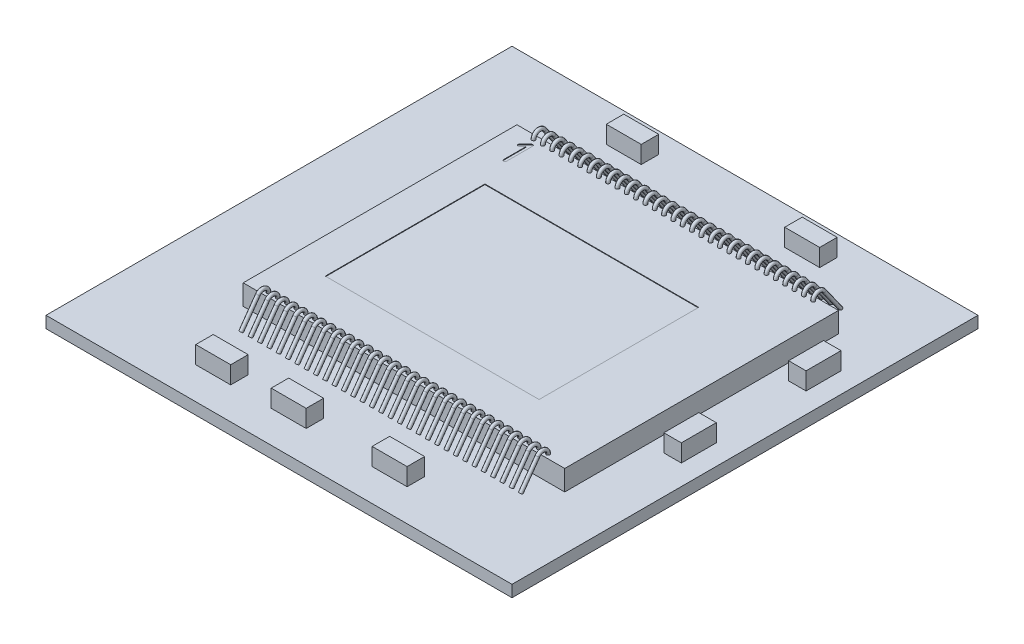
SolidWorks part; units mm, degrees
material "1060 Legierung"
ref_plane "Vorne" through (0, 0, 0) normal (0, 0, 1) x (1, 0, 0)
ref_plane "Oben" through (0, 0, 0) normal (0, 1, 0) x (1, 0, 0)
ref_plane "Rechts" through (0, 0, 0) normal (1, 0, 0) x (0, 0, -1)
ref_plane "Faser-Ebene_Vorne" through (0, 0, 0.175) normal (0, 0, 1) x (1, 0, 0)
ref_plane "Faser-Ebene_Rechts" through (-0.32, 0, 0) normal (1, 0, 0) x (0, 0, -1)
sketch "X-Ray_side"
sketch "Chip_Dimensions"
sketch "Skizze1" plane through (0, 0, 0) normal (0, 1, 0) x (1, 0, 0)
  line L0 (-2.76, 2.35) -> (2.76, -2.35) construction
  line L1 (-2.76, 2.35) -> (2.76, 2.35)
  line L2 (-2.76, 2.35) -> (-2.76, -2.35)
  line L3 (-2.76, -2.35) -> (2.76, -2.35)
  line L4 (2.76, 2.35) -> (2.76, -2.35)
  dimension "D1" = 5.52
  dimension "D2" = 4.7
extrude "Chip_Die" add sketch "Skizze1" along normal blind 0.35
sketch "Skizze4" plane through (0, 0.35, 0) normal (0, 1, 0) x (1, 0, 0)
  line L0 (1.515, 1.195) -> (-2.155, -1.545) construction
  line L1 (-2.155, 1.195) -> (1.515, 1.195)
  line L2 (-2.155, 1.195) -> (-2.155, -1.545)
  line L3 (-2.155, -1.545) -> (1.515, -1.545)
  line L4 (1.515, 1.195) -> (1.515, -1.545)
  line L5 (-0.32, 1.195) -> (-0.32, -0.1113) construction
  line L7 (-0.32, -0.1925) -> (-0.32, 0.1925) construction
  line L8 (1.515, -0.175) -> (0.7734, -0.175) construction
  line L9 (-0.1925, -0.175) -> (0.1925, -0.175) construction
  point P6 (-0.32, -0.175)
  point P7 (0, 0)
  dimension "D1" = 3.67
  dimension "D2" = 2.74
extrude "Active_Area" cut sketch "Skizze4" against normal blind 0.01
sketch "Skizze5" plane through (0, 0.35, 0) normal (0, 1, 0) x (1, 0, 0)
  text T0 "1" font "ISOCPEUR" height 0.5
extrude "Pin1" cut sketch "Skizze5" against normal blind 0.01
sketch "Skizze6" plane through (0, 0, 0) normal (0, 1, 0) x (1, 0, 0)
  line L0 (-2.155, 1.195) -> (1.515, -1.545) construction
  line L1 (-4.32, 3.825) -> (3.68, 3.825)
  line L2 (-4.32, 3.825) -> (-4.32, -4.175)
  line L3 (-4.32, -4.175) -> (3.68, -4.175)
  line L4 (3.68, 3.825) -> (3.68, -4.175)
  line L5 (3.68, 3.825) -> (-4.32, -4.175) construction
  point P7 (-0.32, -0.175)
  dimension "D1" = 8
extrude "Base-Plate" add sketch "Skizze6" against normal blind 0.2
sketch "Skizze12" plane through (0, 0, 0) normal (1, 0, 0) x (0, 0, -1)
  line L0 (-2.35, 0.35) -> (2.35, 0.35) construction
  line L1 (-2.4563, 0.4079) -> (-2.7458, 0)
  line L2 (-4.175, 0) -> (3.825, 0) construction
  line L3 (0, 0) -> (0, 1.1196) construction
  arc A0 (-2.2748, 0.35) -> (-2.4563, 0.4079) centre (-2.3748, 0.35) ccw
  dimension "D1" = 0.1
sketch "Skizze13" plane through (0, 0.35, 0) normal (0, 1, 0) x (1, 0, 0)
  line L0 (0, 0) -> (0, -1.1473) construction
  circle A0 centre (0, -2.2748) radius 0.03
  circle A1 centre (0.16, -2.2748) radius 0.03
  circle A2 centre (0.32, -2.2748) radius 0.03
  circle A3 centre (0.48, -2.2748) radius 0.03
  circle A4 centre (0.64, -2.2748) radius 0.03
  circle A5 centre (0.8, -2.2748) radius 0.03
  circle A6 centre (0.96, -2.2748) radius 0.03
  circle A7 centre (1.12, -2.2748) radius 0.03
  circle A8 centre (1.28, -2.2748) radius 0.03
  circle A9 centre (1.44, -2.2748) radius 0.03
  circle A10 centre (1.6, -2.2748) radius 0.03
  circle A11 centre (1.76, -2.2748) radius 0.03
  circle A12 centre (1.92, -2.2748) radius 0.03
  circle A13 centre (2.08, -2.2748) radius 0.03
  circle A14 centre (2.24, -2.2748) radius 0.03
  circle A15 centre (2.4, -2.2748) radius 0.03
  circle A16 centre (-2.4, -2.2748) radius 0.03
  circle A17 centre (-2.24, -2.2748) radius 0.03
  circle A18 centre (-2.08, -2.2748) radius 0.03
  circle A19 centre (-1.92, -2.2748) radius 0.03
  circle A20 centre (-1.76, -2.2748) radius 0.03
  circle A21 centre (-1.6, -2.2748) radius 0.03
  circle A22 centre (-1.44, -2.2748) radius 0.03
  circle A23 centre (-1.28, -2.2748) radius 0.03
  circle A24 centre (-1.12, -2.2748) radius 0.03
  circle A25 centre (-0.96, -2.2748) radius 0.03
  circle A26 centre (-0.8, -2.2748) radius 0.03
  circle A27 centre (-0.64, -2.2748) radius 0.03
  circle A28 centre (-0.48, -2.2748) radius 0.03
  circle A29 centre (-0.32, -2.2748) radius 0.03
  circle A30 centre (-0.16, -2.2748) radius 0.03
  dimension "D1" = 0.06
  dimension "D2" = 16
sweep "Bonding-wires" add profiles "Skizze13" path "Skizze12"
mirror "Spiegeln1" about plane through (0, 0, 0) normal (0, 0, 1) of "Bonding-wires"
sketch "X-Ray_top"
sketch "Skizze14" plane through (0, 0, 0) normal (0, 1, 0) x (1, 0, 0)
  line L0 (-4.32, -4.175) -> (3.68, -4.175) construction
  line L1 (-2.2994, -3.325) -> (-1.6994, -3.325)
  line L2 (-2.2994, -3.325) -> (-2.2994, -3.625)
  line L3 (-2.2994, -3.625) -> (-1.6994, -3.625)
  line L4 (-1.6994, -3.325) -> (-1.6994, -3.625)
  line L5 (3.68, -4.175) -> (3.68, 3.825) construction
  line L6 (-1.0036, -3.325) -> (-0.4036, -3.325)
  line L7 (-1.0036, -3.325) -> (-1.0036, -3.625)
  line L8 (-1.0036, -3.625) -> (-0.4036, -3.625)
  line L9 (-0.4036, -3.325) -> (-0.4036, -3.625)
  line L10 (0.7291, -3.625) -> (1.3291, -3.625)
  line L11 (0.7291, -3.625) -> (0.7291, -3.325)
  line L12 (0.7291, -3.325) -> (1.3291, -3.325)
  line L13 (1.3291, -3.625) -> (1.3291, -3.325)
  line L14 (3.03, -0.3181) -> (3.33, -0.3181)
  line L15 (3.03, -0.3181) -> (3.03, -0.9181)
  line L16 (3.03, -0.9181) -> (3.33, -0.9181)
  line L17 (3.33, -0.3181) -> (3.33, -0.9181)
  line L18 (3.68, 3.825) -> (-4.32, 3.825) construction
  line L19 (3.03, 1.2236) -> (3.33, 1.2236)
  line L20 (3.03, 1.2236) -> (3.03, 1.8236)
  line L21 (3.03, 1.8236) -> (3.33, 1.8236)
  line L22 (3.33, 1.2236) -> (3.33, 1.8236)
  line L23 (-1.4515, 3.175) -> (-2.0515, 3.175)
  line L24 (-1.4515, 3.175) -> (-1.4515, 3.475)
  line L25 (-1.4515, 3.475) -> (-2.0515, 3.475)
  line L26 (-2.0515, 3.175) -> (-2.0515, 3.475)
  line L28 (1.012, 3.475) -> (1.612, 3.475)
  line L29 (1.012, 3.475) -> (1.012, 3.175)
  line L30 (1.012, 3.175) -> (1.612, 3.175)
  line L31 (1.612, 3.475) -> (1.612, 3.175)
  dimension "D1" = 0.3
  dimension "D2" = 0.6
  dimension "D3" = 0.55
  dimension "D4" = 0.35
  dimension "D5" = 0.35
extrude "Electronic_components" add sketch "Skizze14" along normal blind 0.3
ref_point "Point1"
